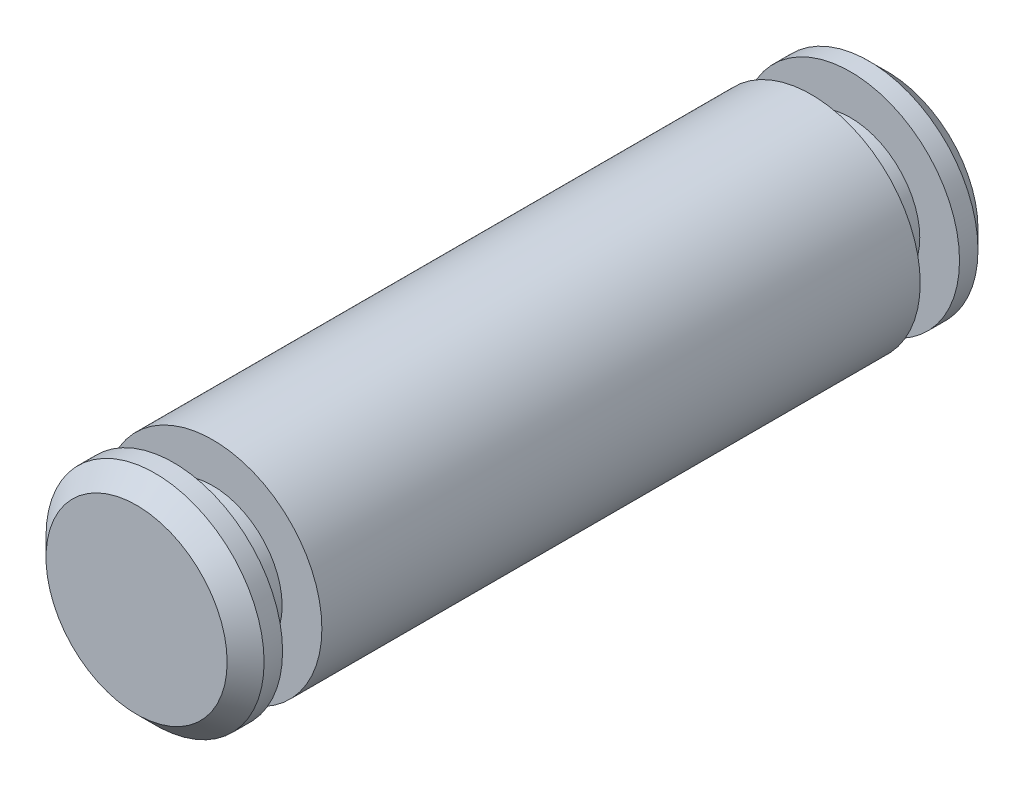
SolidWorks part; units mm, degrees
material "AISI Type A2 Tool Steel"
ref_plane "Front Plane" through (0, 0, 0) normal (0, 0, 1) x (1, 0, 0)
ref_plane "Top Plane" through (0, 0, 0) normal (0, 1, 0) x (1, 0, 0)
ref_plane "Right Plane" through (0, 0, 0) normal (1, 0, 0) x (0, 0, -1)
sketch "Sketch1" plane through (0, 0, 0) normal (0, 0, 1) x (1, 0, 0)
  circle A0 centre (0, 0) radius 1.4986
  dimension "D1" = 2.9972
extrude "Boss-Extrude1" add sketch "Sketch1" along normal mid plane 10.3187
sketch "Sketch2" plane through (0, 0, 0) normal (1, 0, 0) x (0, 0, -1)
  line L0 (-5.1594, -1.4986) -> (5.1594, -1.4986) construction
  line L1 (-4.6514, -1.4986) -> (-4.1114, -1.4986)
  line L2 (-4.6514, -1.4986) -> (-4.6514, -0.9525)
  line L3 (-4.6514, -0.9525) -> (-4.1114, -0.9525)
  line L4 (-4.1114, -1.4986) -> (-4.1114, -0.9525)
  line L5 (-5.1594, 1.4986) -> (-5.1594, -1.4986) construction
  line L6 (-8.828, 0) -> (8.9454, 0) construction
  line L7 (1.6485, 0) -> (-1.6485, 0) construction
  line L8 (0, 2.428) -> (0, -3.7184) construction
  line L9 (4.1114, -1.4986) -> (4.1114, -0.9525)
  line L10 (4.6514, -0.9525) -> (4.1114, -0.9525)
  line L11 (4.6514, -1.4986) -> (4.6514, -0.9525)
  line L12 (4.6514, -1.4986) -> (4.1114, -1.4986)
  dimension "D1" = 0.508
  dimension "D2" = 0.54
  dimension "D3" = 1.905
revolve "Cut-Revolve1" cut sketch "Sketch2" angle 360 about L6
chamfer "Chamfer1" distance 0.254 angle 45
